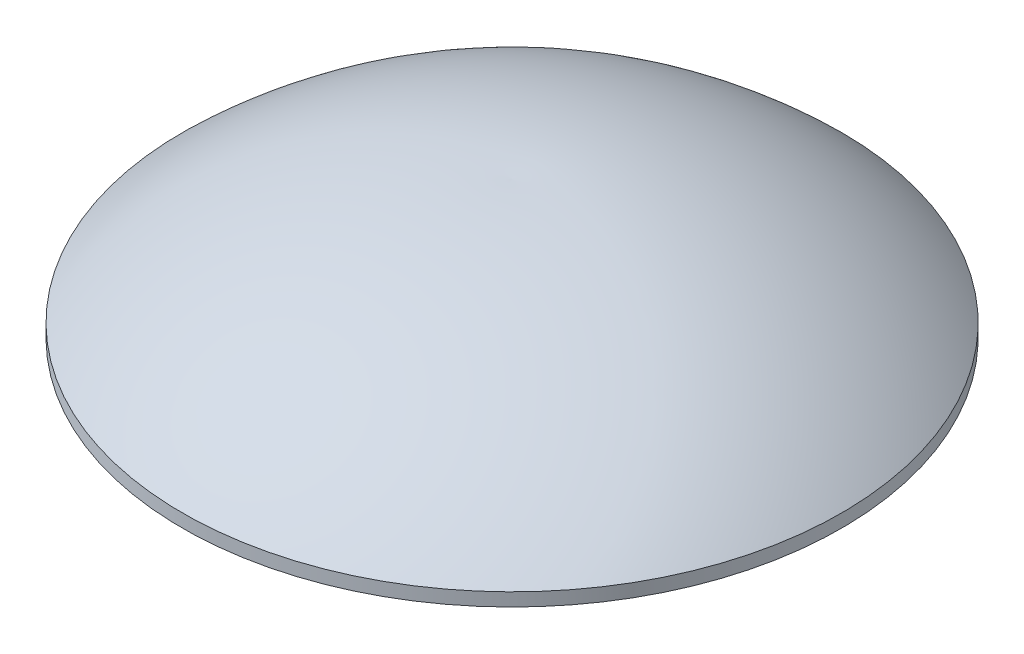
SolidWorks part; units mm, degrees
ref_plane "Front Plane" through (0, 0, 0) normal (0, 0, 1) x (1, 0, 0)
ref_plane "Top Plane" through (0, 0, 0) normal (0, 1, 0) x (1, 0, 0)
ref_plane "Right Plane" through (0, 0, 0) normal (1, 0, 0) x (0, 0, -1)
sketch "Sketch1" plane through (0, 0, 0) normal (0, 0, 1) x (1, 0, 0)
  line L1 (-3.1798, -0.107) -> (0.2706, 1.7) construction
  line L2 (-2.5, 0.1) -> (-2.5, 0)
  line L3 (-2.5, 0) -> (0, 0)
  line L5 (0, 0) -> (0, 1.0465)
  arc A0 (-2.5, 0.1) -> (0, 1.0465) centre (-0.1246, -2.3991) cw
  dimension "D1" = 2.5
  dimension "D2" = 0.1
  dimension "D3" = 1.6
sketch "Sketch2" plane through (0, 0, 0) normal (0, 0, 1) x (1, 0, 0)
  line L0 (0, -0.5356) -> (0, 1.8652) construction
revolve "Revolve1" add sketch "Sketch1" angle 360 about L0
